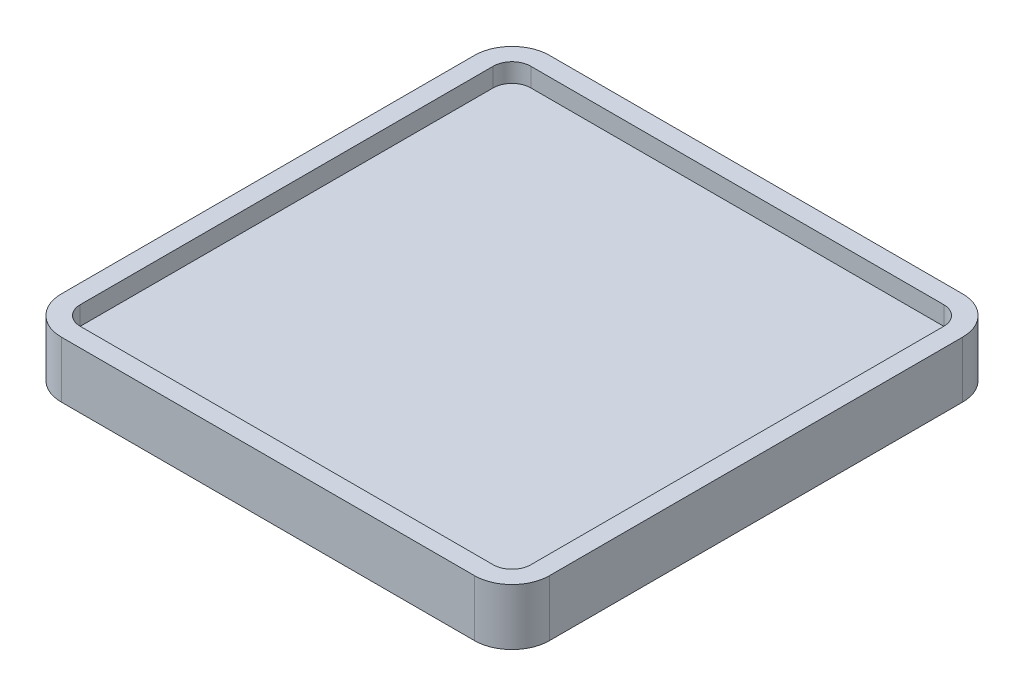
SolidWorks part; units mm, degrees
ref_plane "Front Plane" through (0, 0, 0) normal (0, 0, 1) x (1, 0, 0)
ref_plane "Top Plane" through (0, 0, 0) normal (0, 1, 0) x (1, 0, 0)
ref_plane "Right Plane" through (0, 0, 0) normal (1, 0, 0) x (0, 0, -1)
sketch "Sketch1" plane through (0, 0, 0) normal (0, 1, 0) x (1, 0, 0)
  line L0 (0, 55.3318) -> (0, -54.7021) construction
  line L1 (0, -55) -> (0, 55) construction
  line L2 (-35.2755, 0) -> (43.3038, 0) construction
  line L3 (-11, 12) -> (11, 12)
  line L4 (-12, 11) -> (-12, -11)
  line L5 (-11, -12) -> (11, -12)
  line L6 (12, 11) -> (12, -11)
  line L7 (-13, 11) -> (-13, -11)
  line L8 (-11, -13) -> (11, -13)
  line L9 (13, 11) -> (13, -11)
  line L10 (-11, 13) -> (11, 13)
  arc A0 (-12, -11) -> (-11, -12) centre (-11, -11) ccw
  arc A1 (11, -12) -> (12, -11) centre (11, -11) ccw
  arc A2 (12, 11) -> (11, 12) centre (11, 11) ccw
  arc A3 (-11, 12) -> (-12, 11) centre (-11, 11) ccw
  arc A4 (-13, -11) -> (-11, -13) centre (-11, -11) ccw
  arc A5 (11, -13) -> (13, -11) centre (11, -11) ccw
  arc A6 (13, 11) -> (11, 13) centre (11, 11) ccw
  arc A7 (-11, 13) -> (-13, 11) centre (-11, 11) ccw
  point P13 (-12, -12)
  point P16 (12, -12)
  point P19 (12, 12)
  dimension "D3" = 1
  dimension "D1" = 24
  dimension "D2" = 24
  dimension "D4" = 1
extrude "Boss-Extrude1" add sketch "Sketch1" along normal blind 1
sketch "Sketch2" plane through (0, 0, 0) normal (0, -1, 0) x (1, 0, 0)
  line L4 (-11, -13) -> (11, -13)
  line L5 (13, -11) -> (13, 11)
  line L6 (11, 13) -> (-11, 13)
  line L7 (-13, 11) -> (-13, -11)
  line L8 (-11, -13) -> (11, -13)
  line L9 (13, -11) -> (13, 11)
  line L10 (11, 13) -> (-11, 13)
  line L11 (-13, 11) -> (-13, -11)
  arc A4 (-13, -11) -> (-11, -13) centre (-11, -11) ccw
  arc A5 (11, -13) -> (13, -11) centre (11, -11) ccw
  arc A6 (13, 11) -> (11, 13) centre (11, 11) ccw
  arc A7 (-11, 13) -> (-13, 11) centre (-11, 11) ccw
  arc A8 (-13, -11) -> (-11, -13) centre (-11, -11) ccw
  arc A9 (11, -13) -> (13, -11) centre (11, -11) ccw
  arc A10 (13, 11) -> (11, 13) centre (11, 11) ccw
  arc A11 (-11, 13) -> (-13, 11) centre (-11, 11) ccw
  dimension "D1" = 0
extrude "Boss-Extrude2" add sketch "Sketch2" along normal blind 2
